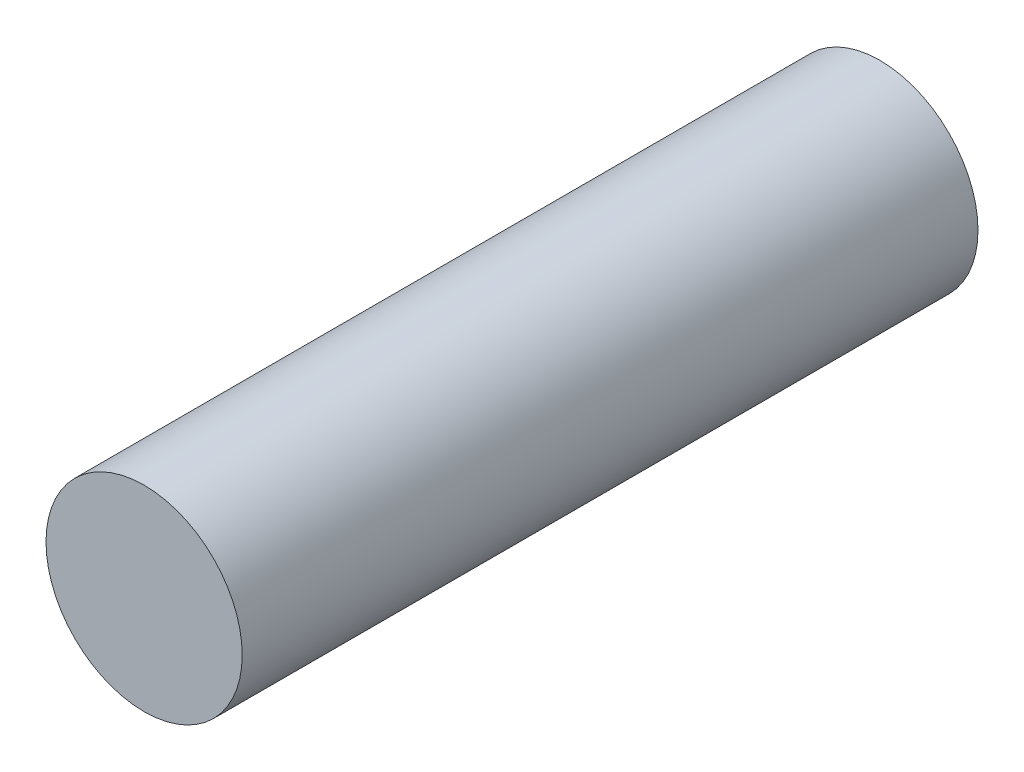
SolidWorks part; units mm, degrees
ref_plane "Front Plane" through (0, 0, 0) normal (0, 0, 1) x (1, 0, 0)
ref_plane "Top Plane" through (0, 0, 0) normal (0, 1, 0) x (1, 0, 0)
ref_plane "Right Plane" through (0, 0, 0) normal (1, 0, 0) x (0, 0, -1)
sketch "Sketch1" plane through (0, 0, 0) normal (0, 0, 1) x (1, 0, 0)
  circle A0 centre (0, 0) radius 4
  dimension "D1" = 8
extrude "Boss-Extrude1" add sketch "Sketch1" along normal blind 30
